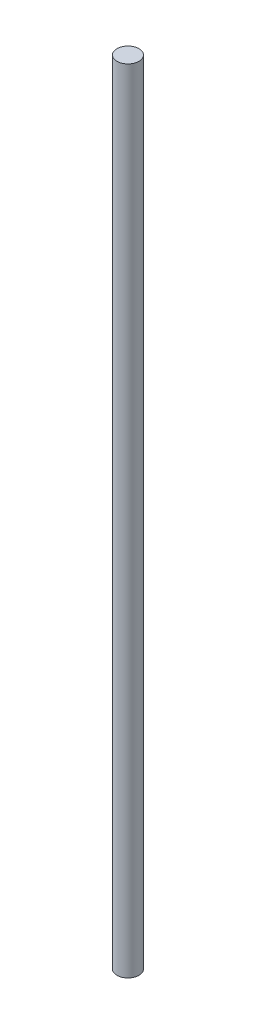
SolidWorks part; units mm, degrees
ref_plane "Front Plane" through (0, 0, 0) normal (0, 0, 1) x (1, 0, 0)
ref_plane "Top Plane" through (0, 0, 0) normal (0, 1, 0) x (1, 0, 0)
ref_plane "Right Plane" through (0, 0, 0) normal (1, 0, 0) x (0, 0, -1)
sketch "Sketch1" plane through (0, 0, 0) normal (0, 1, 0) x (1, 0, 0)
  circle A0 centre (0, 0) radius 3.175
  dimension "D1" = 6.35
extrude "Boss-Extrude1" add sketch "Sketch1" along normal blind 228.6
